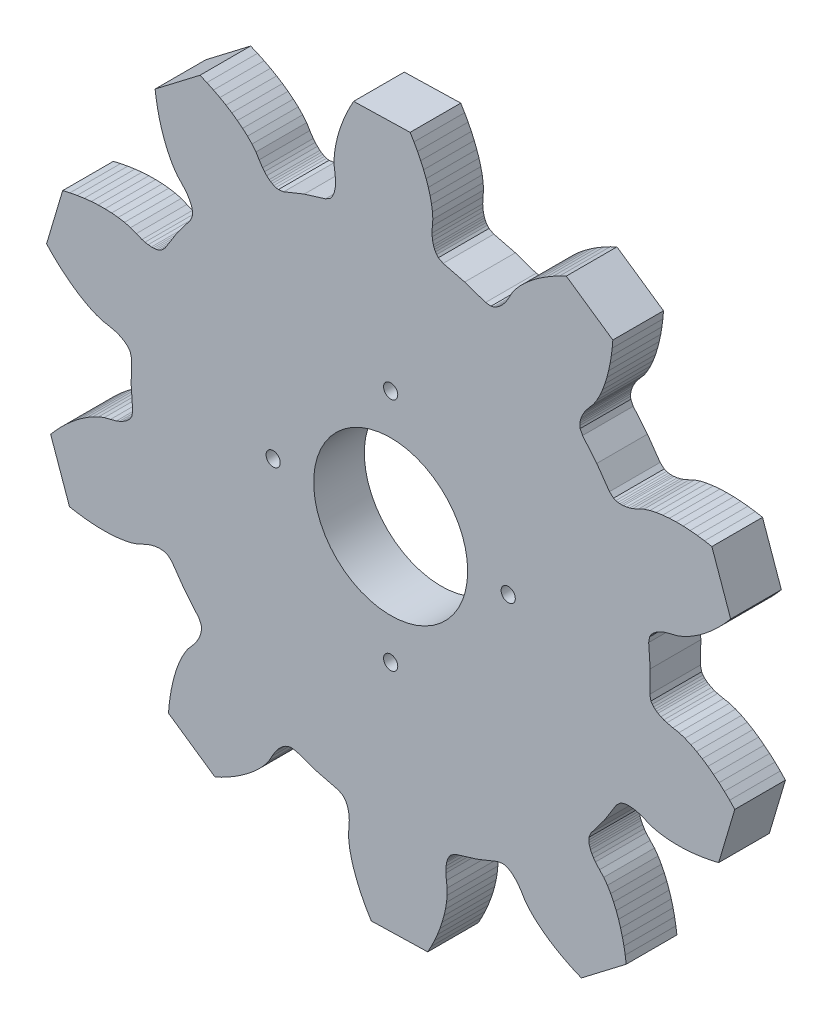
SolidWorks part; units mm, degrees
ref_plane "Front Plane" through (0, 0, 0) normal (0, 0, 1) x (1, 0, 0)
ref_plane "Top Plane" through (0, 0, 0) normal (0, 1, 0) x (1, 0, 0)
ref_plane "Right Plane" through (0, 0, 0) normal (1, 0, 0) x (0, 0, -1)
sketch "Sketch1" plane through (0, 0, 0) normal (0, 0, 1) x (1, 0, 0)
  line L2 (5.8044, 23.0223) -> (5.7313, 23.3545)
  line L3 (5.7313, 23.3545) -> (5.6459, 23.4886)
  line L4 (5.6459, 23.4886) -> (5.5583, 23.5882)
  line L5 (5.5583, 23.5882) -> (5.4694, 23.6692)
  line L6 (5.4694, 23.6692) -> (5.3795, 23.7376)
  line L7 (5.3795, 23.7376) -> (5.2888, 23.797)
  line L8 (5.2888, 23.797) -> (5.1059, 23.8948)
  line L9 (5.1059, 23.8948) -> (4.9207, 23.972)
  line L10 (4.9207, 23.972) -> (4.7338, 24.0332)
  line L11 (4.7338, 24.0332) -> (4.3561, 24.1183)
  line L12 (4.3561, 24.1183) -> (3.9766, 24.1866)
  line L13 (3.9766, 24.1866) -> (3.604, 24.3114)
  line L14 (3.604, 24.3114) -> (3.2362, 24.4721)
  line L15 (3.2362, 24.4721) -> (2.873, 24.6616)
  line L16 (2.873, 24.6616) -> (2.5143, 24.876)
  line L17 (2.5143, 24.876) -> (2.1605, 25.1137)
  line L18 (2.1605, 25.1137) -> (1.812, 25.3731)
  line L19 (1.812, 25.3731) -> (1.4691, 25.6527)
  line L20 (1.4691, 25.6527) -> (1.1323, 25.9524)
  line L21 (1.1323, 25.9524) -> (0.8016, 26.2707)
  line L22 (0.8016, 26.2707) -> (0.4778, 26.6078)
  line L23 (0.4778, 26.6078) -> (1.4874, 30.0037)
  line L24 (1.4874, 30.0037) -> (1.9428, 30.1089)
  line L25 (1.9428, 30.1089) -> (2.3937, 30.195)
  line L26 (2.3937, 30.195) -> (2.8397, 30.2616)
  line L27 (2.8397, 30.2616) -> (3.2796, 30.3085)
  line L28 (3.2796, 30.3085) -> (3.7132, 30.3355)
  line L29 (3.7132, 30.3355) -> (4.1394, 30.3411)
  line L30 (4.1394, 30.3411) -> (4.557, 30.3251)
  line L31 (4.557, 30.3251) -> (4.9647, 30.2852)
  line L32 (4.9647, 30.2852) -> (5.3604, 30.2189)
  line L33 (5.3604, 30.2189) -> (5.7409, 30.1196)
  line L34 (5.7409, 30.1196) -> (6.096, 29.9695)
  line L35 (6.096, 29.9695) -> (6.459, 29.8343)
  line L36 (6.459, 29.8343) -> (6.6487, 29.7835)
  line L37 (6.6487, 29.7835) -> (6.8461, 29.747)
  line L38 (6.8461, 29.747) -> (7.0528, 29.7289)
  line L39 (7.0528, 29.7289) -> (7.161, 29.7292)
  line L40 (7.161, 29.7292) -> (7.2738, 29.7373)
  line L41 (7.2738, 29.7373) -> (7.3924, 29.7566)
  line L42 (7.3924, 29.7566) -> (7.5204, 29.7922)
  line L43 (7.5204, 29.7922) -> (7.665, 29.858)
  line L44 (7.665, 29.858) -> (7.9078, 30.0962)
  line L45 (7.9078, 30.0962) -> (8.6457, 31.2717)
  line L46 (8.6457, 31.2717) -> (9.4811, 32.3804)
  line L47 (9.4811, 32.3804) -> (9.6172, 32.6921)
  line L48 (9.6172, 32.6921) -> (9.6271, 32.8506)
  line L49 (9.6271, 32.8506) -> (9.6149, 32.9827)
  line L50 (9.6149, 32.9827) -> (9.5905, 33.1005)
  line L51 (9.5905, 33.1005) -> (9.558, 33.2087)
  line L52 (9.558, 33.2087) -> (9.5194, 33.3101)
  line L53 (9.5194, 33.3101) -> (9.429, 33.4968)
  line L54 (9.429, 33.4968) -> (9.3246, 33.6682)
  line L55 (9.3246, 33.6682) -> (9.2093, 33.8275)
  line L56 (9.2093, 33.8275) -> (8.9538, 34.1183)
  line L57 (8.9538, 34.1183) -> (8.6868, 34.3967)
  line L58 (8.6868, 34.3967) -> (8.4587, 34.7165)
  line L59 (8.4587, 34.7165) -> (8.2555, 35.0629)
  line L60 (8.2555, 35.0629) -> (8.0731, 35.4294)
  line L61 (8.0731, 35.4294) -> (7.9091, 35.814)
  line L62 (7.9091, 35.814) -> (7.7627, 36.2141)
  line L63 (7.7627, 36.2141) -> (7.6332, 36.6286)
  line L64 (7.6332, 36.6286) -> (7.5202, 37.0566)
  line L65 (7.5202, 37.0566) -> (7.4237, 37.497)
  line L66 (7.4237, 37.497) -> (7.3434, 37.9489)
  line L67 (7.3434, 37.9489) -> (7.2794, 38.4119)
  line L68 (7.2794, 38.4119) -> (10.0924, 40.5658)
  line L69 (10.0924, 40.5658) -> (10.5225, 40.3832)
  line L70 (10.5225, 40.3832) -> (10.938, 40.1879)
  line L71 (10.938, 40.1879) -> (11.3378, 39.9796)
  line L72 (11.3378, 39.9796) -> (11.7216, 39.7589)
  line L73 (11.7216, 39.7589) -> (12.0881, 39.5257)
  line L74 (12.0881, 39.5257) -> (12.4361, 39.2801)
  line L75 (12.4361, 39.2801) -> (12.7645, 39.0215)
  line L76 (12.7645, 39.0215) -> (13.0708, 38.7497)
  line L77 (13.0708, 38.7497) -> (13.352, 38.4632)
  line L78 (13.352, 38.4632) -> (13.6014, 38.1597)
  line L79 (13.6014, 38.1597) -> (13.8006, 37.8292)
  line L80 (13.8006, 37.8292) -> (14.0147, 37.5067)
  line L81 (14.0147, 37.5067) -> (14.1384, 37.354)
  line L82 (14.1384, 37.354) -> (14.2766, 37.2085)
  line L83 (14.2766, 37.2085) -> (14.4333, 37.0723)
  line L84 (14.4333, 37.0723) -> (14.5209, 37.0088)
  line L85 (14.5209, 37.0088) -> (14.6169, 36.9491)
  line L86 (14.6169, 36.9491) -> (14.7244, 36.895)
  line L87 (14.7244, 36.895) -> (14.8486, 36.8485)
  line L88 (14.8486, 36.8485) -> (15.0043, 36.8168)
  line L89 (15.0043, 36.8168) -> (15.3408, 36.8668)
  line L90 (15.3408, 36.8668) -> (16.6289, 37.3842)
  line L91 (16.6289, 37.3842) -> (17.9563, 37.7899)
  line L92 (17.9563, 37.7899) -> (18.2496, 37.9621)
  line L93 (18.2496, 37.9621) -> (18.3507, 38.0848)
  line L94 (18.3507, 38.0848) -> (18.4186, 38.1988)
  line L95 (18.4186, 38.1988) -> (18.4681, 38.3083)
  line L96 (18.4681, 38.3083) -> (18.5054, 38.415)
  line L97 (18.5054, 38.415) -> (18.5336, 38.5196)
  line L98 (18.5336, 38.5196) -> (18.5702, 38.7238)
  line L99 (18.5702, 38.7238) -> (18.5864, 38.9237)
  line L100 (18.5864, 38.9237) -> (18.587, 39.1203)
  line L101 (18.587, 39.1203) -> (18.5511, 39.5059)
  line L102 (18.5511, 39.5059) -> (18.4988, 39.8879)
  line L103 (18.4988, 39.8879) -> (18.5024, 40.2811)
  line L104 (18.5024, 40.2811) -> (18.5415, 40.6804)
  line L105 (18.5415, 40.6804) -> (18.6093, 41.0845)
  line L106 (18.6093, 41.0845) -> (18.7028, 41.4917)
  line L107 (18.7028, 41.4917) -> (18.8194, 41.9016)
  line L108 (18.8194, 41.9016) -> (18.9583, 42.3131)
  line L109 (18.9583, 42.3131) -> (19.1183, 42.7258)
  line L110 (19.1183, 42.7258) -> (19.2992, 43.1389)
  line L111 (19.2992, 43.1389) -> (19.4998, 43.5516)
  line L112 (19.4998, 43.5516) -> (19.7203, 43.9638)
  line L113 (19.7203, 43.9638) -> (23.2621, 44.0527)
  line L114 (23.2621, 44.0527) -> (23.5029, 43.6522)
  line L115 (23.5029, 43.6522) -> (23.7241, 43.2501)
  line L116 (23.7241, 43.2501) -> (23.9253, 42.8465)
  line L117 (23.9253, 42.8465) -> (24.1059, 42.4426)
  line L118 (24.1059, 42.4426) -> (24.2651, 42.0385)
  line L119 (24.2651, 42.0385) -> (24.4025, 41.6352)
  line L120 (24.4025, 41.6352) -> (24.5161, 41.2328)
  line L121 (24.5161, 41.2328) -> (24.6042, 40.8328)
  line L122 (24.6042, 40.8328) -> (24.6634, 40.436)
  line L123 (24.6634, 40.436) -> (24.6868, 40.0436)
  line L124 (24.6868, 40.0436) -> (24.6535, 39.6593)
  line L125 (24.6535, 39.6593) -> (24.6372, 39.2725)
  line L126 (24.6372, 39.2725) -> (24.6477, 39.0761)
  line L127 (24.6477, 39.0761) -> (24.6738, 38.8772)
  line L128 (24.6738, 38.8772) -> (24.7205, 38.6751)
  line L129 (24.7205, 38.6751) -> (24.7541, 38.5722)
  line L130 (24.7541, 38.5722) -> (24.7967, 38.4675)
  line L131 (24.7967, 38.4675) -> (24.8516, 38.3606)
  line L132 (24.8516, 38.3606) -> (24.925, 38.2499)
  line L133 (24.925, 38.2499) -> (25.0322, 38.1325)
  line L134 (25.0322, 38.1325) -> (25.334, 37.9753)
  line L135 (25.334, 37.9753) -> (26.6802, 37.637)
  line L136 (26.6802, 37.637) -> (27.9926, 37.1848)
  line L137 (27.9926, 37.1848) -> (28.3309, 37.1518)
  line L138 (28.3309, 37.1518) -> (28.4848, 37.1914)
  line L139 (28.4848, 37.1914) -> (28.6067, 37.244)
  line L140 (28.6067, 37.244) -> (28.7111, 37.3035)
  line L141 (28.7111, 37.3035) -> (28.8041, 37.3677)
  line L142 (28.8041, 37.3677) -> (28.8884, 37.4358)
  line L143 (28.8884, 37.4358) -> (29.0383, 37.5796)
  line L144 (29.0383, 37.5796) -> (29.1689, 37.7317)
  line L145 (29.1689, 37.7317) -> (29.2847, 37.8905)
  line L146 (29.2847, 37.8905) -> (29.4823, 38.2234)
  line L147 (29.4823, 38.2234) -> (29.6647, 38.5633)
  line L148 (29.6647, 38.5633) -> (29.8983, 38.8793)
  line L149 (29.8983, 38.8793) -> (30.165, 39.1795)
  line L150 (30.165, 39.1795) -> (30.4574, 39.4663)
  line L151 (30.4574, 39.4663) -> (30.7724, 39.7411)
  line L152 (30.7724, 39.7411) -> (31.1076, 40.004)
  line L153 (31.1076, 40.004) -> (31.4617, 40.2552)
  line L154 (31.4617, 40.2552) -> (31.8338, 40.495)
  line L155 (31.8338, 40.495) -> (32.2229, 40.7228)
  line L156 (32.2229, 40.7228) -> (32.6278, 40.939)
  line L157 (32.6278, 40.939) -> (33.0484, 41.1427)
  line L158 (33.0484, 41.1427) -> (35.9661, 39.133)
  line L159 (35.9661, 39.133) -> (35.9255, 38.6674)
  line L160 (35.9255, 38.6674) -> (35.8681, 38.212)
  line L161 (35.8681, 38.212) -> (35.7937, 37.7673)
  line L162 (35.7937, 37.7673) -> (35.7022, 37.3342)
  line L163 (35.7022, 37.3342) -> (35.5938, 36.9136)
  line L164 (35.5938, 36.9136) -> (35.4675, 36.5067)
  line L165 (35.4675, 36.5067) -> (35.3233, 36.1145)
  line L166 (35.3233, 36.1145) -> (35.1594, 35.7391)
  line L167 (35.1594, 35.7391) -> (34.974, 35.3832)
  line L168 (34.974, 35.3832) -> (34.7622, 35.052)
  line L169 (34.7622, 35.052) -> (34.5095, 34.7607)
  line L170 (34.5095, 34.7607) -> (34.2689, 34.4574)
  line L171 (34.2689, 34.4574) -> (34.162, 34.2925)
  line L172 (34.162, 34.2925) -> (34.0662, 34.1163)
  line L173 (34.0662, 34.1163) -> (33.9852, 33.925)
  line L174 (33.9852, 33.925) -> (33.9517, 33.8219)
  line L175 (33.9517, 33.8219) -> (33.9247, 33.7121)
  line L176 (33.9247, 33.7121) -> (33.9065, 33.5935)
  line L177 (33.9065, 33.5935) -> (33.9006, 33.4609)
  line L178 (33.9006, 33.4609) -> (33.9187, 33.303)
  line L179 (33.9187, 33.303) -> (34.07, 32.9984)
  line L180 (34.07, 32.9984) -> (34.9603, 31.9334)
  line L181 (34.9603, 31.9334) -> (35.7563, 30.7962)
  line L182 (35.7563, 30.7962) -> (36.0106, 30.5704)
  line L183 (36.0106, 30.5704) -> (36.1584, 30.512)
  line L184 (36.1584, 30.512) -> (36.288, 30.4828)
  line L185 (36.288, 30.4828) -> (36.4076, 30.4696)
  line L186 (36.4076, 30.4696) -> (36.5204, 30.467)
  line L187 (36.5204, 30.467) -> (36.6286, 30.4724)
  line L188 (36.6286, 30.4724) -> (36.8343, 30.5008)
  line L189 (36.8343, 30.5008) -> (37.0294, 30.5473)
  line L190 (37.0294, 30.5473) -> (37.2166, 30.6075)
  line L191 (37.2166, 30.6075) -> (37.5722, 30.7607)
  line L192 (37.5722, 30.7607) -> (37.9194, 30.9286)
  line L193 (37.9194, 30.9286) -> (38.2941, 31.0467)
  line L194 (38.2941, 31.0467) -> (38.6862, 31.1328)
  line L195 (38.6862, 31.1328) -> (39.0914, 31.193)
  line L196 (39.0914, 31.193) -> (39.5077, 31.2303)
  line L197 (39.5077, 31.2303) -> (39.9334, 31.2458)
  line L198 (39.9334, 31.2458) -> (40.3677, 31.241)
  line L199 (40.3677, 31.241) -> (40.8097, 31.2161)
  line L200 (40.8097, 31.2161) -> (41.2582, 31.1719)
  line L201 (41.2582, 31.1719) -> (41.7131, 31.1086)
  line L202 (41.7131, 31.1086) -> (42.1731, 31.0264)
  line L203 (42.1731, 31.0264) -> (43.3522, 27.6855)
  line L204 (43.3522, 27.6855) -> (43.0456, 27.3327)
  line L205 (43.0456, 27.3327) -> (42.7314, 26.9982)
  line L206 (42.7314, 26.9982) -> (42.4099, 26.6819)
  line L207 (42.4099, 26.6819) -> (42.0814, 26.3853)
  line L208 (42.0814, 26.3853) -> (41.7464, 26.1089)
  line L209 (41.7464, 26.1089) -> (41.4053, 25.8536)
  line L210 (41.4053, 25.8536) -> (41.0578, 25.6215)
  line L211 (41.0578, 25.6215) -> (40.7045, 25.414)
  line L212 (40.7045, 25.414) -> (40.3454, 25.2349)
  line L213 (40.3454, 25.2349) -> (39.9793, 25.0916)
  line L214 (39.9793, 25.0916) -> (39.6037, 25.0043)
  line L215 (39.6037, 25.0043) -> (39.2308, 24.9004)
  line L216 (39.2308, 24.9004) -> (39.0474, 24.83)
  line L217 (39.0474, 24.83) -> (38.8663, 24.7434)
  line L218 (38.8663, 24.7434) -> (38.6883, 24.6365)
  line L219 (38.6883, 24.6365) -> (38.6009, 24.5727)
  line L220 (38.6009, 24.5727) -> (38.5145, 24.4998)
  line L221 (38.5145, 24.4998) -> (38.4297, 24.4145)
  line L222 (38.4297, 24.4145) -> (38.3471, 24.3106)
  line L223 (38.3471, 24.3106) -> (38.2689, 24.1724)
  line L224 (38.2689, 24.1724) -> (38.2125, 23.8369)
  line L225 (38.2125, 23.8369) -> (38.3065, 22.4521)
  line L226 (38.3065, 22.4521) -> (38.2821, 21.0642)
  line L227 (38.2821, 21.0642) -> (38.3553, 20.732)
  line L228 (38.3553, 20.732) -> (38.4406, 20.5979)
  line L229 (38.4406, 20.5979) -> (38.5282, 20.4983)
  line L230 (38.5282, 20.4983) -> (38.6171, 20.4173)
  line L231 (38.6171, 20.4173) -> (38.7071, 20.349)
  line L232 (38.7071, 20.349) -> (38.7977, 20.2895)
  line L233 (38.7977, 20.2895) -> (38.9806, 20.1917)
  line L234 (38.9806, 20.1917) -> (39.1658, 20.1145)
  line L235 (39.1658, 20.1145) -> (39.3527, 20.0533)
  line L236 (39.3527, 20.0533) -> (39.7304, 19.9682)
  line L237 (39.7304, 19.9682) -> (40.1099, 19.8999)
  line L238 (40.1099, 19.8999) -> (40.4825, 19.7752)
  line L239 (40.4825, 19.7752) -> (40.8503, 19.6144)
  line L240 (40.8503, 19.6144) -> (41.2135, 19.4249)
  line L241 (41.2135, 19.4249) -> (41.5722, 19.2105)
  line L242 (41.5722, 19.2105) -> (41.9257, 18.9728)
  line L243 (41.9257, 18.9728) -> (42.2745, 18.7134)
  line L244 (42.2745, 18.7134) -> (42.6174, 18.4338)
  line L245 (42.6174, 18.4338) -> (42.9542, 18.1341)
  line L246 (42.9542, 18.1341) -> (43.2849, 17.8158)
  line L247 (43.2849, 17.8158) -> (43.6088, 17.4788)
  line L248 (43.6088, 17.4788) -> (42.5988, 14.0828)
  line L249 (42.5988, 14.0828) -> (42.1437, 13.9776)
  line L250 (42.1437, 13.9776) -> (41.6928, 13.8915)
  line L251 (41.6928, 13.8915) -> (41.2468, 13.825)
  line L252 (41.2468, 13.825) -> (40.8069, 13.778)
  line L253 (40.8069, 13.778) -> (40.3733, 13.7511)
  line L254 (40.3733, 13.7511) -> (39.9471, 13.7455)
  line L255 (39.9471, 13.7455) -> (39.5295, 13.7615)
  line L256 (39.5295, 13.7615) -> (39.1218, 13.8013)
  line L257 (39.1218, 13.8013) -> (38.7261, 13.8676)
  line L258 (38.7261, 13.8676) -> (38.3456, 13.967)
  line L259 (38.3456, 13.967) -> (37.9905, 14.1171)
  line L260 (37.9905, 14.1171) -> (37.6276, 14.2522)
  line L261 (37.6276, 14.2522) -> (37.4378, 14.303)
  line L262 (37.4378, 14.303) -> (37.2405, 14.3396)
  line L263 (37.2405, 14.3396) -> (37.0337, 14.3576)
  line L264 (37.0337, 14.3576) -> (36.9255, 14.3574)
  line L265 (36.9255, 14.3574) -> (36.8127, 14.3492)
  line L266 (36.8127, 14.3492) -> (36.6941, 14.3299)
  line L267 (36.6941, 14.3299) -> (36.5661, 14.2944)
  line L268 (36.5661, 14.2944) -> (36.4216, 14.2286)
  line L269 (36.4216, 14.2286) -> (36.1787, 13.9903)
  line L270 (36.1787, 13.9903) -> (35.4409, 12.8148)
  line L271 (35.4409, 12.8148) -> (34.6055, 11.7061)
  line L272 (34.6055, 11.7061) -> (34.4693, 11.3944)
  line L273 (34.4693, 11.3944) -> (34.4594, 11.2359)
  line L274 (34.4594, 11.2359) -> (34.4716, 11.1039)
  line L275 (34.4716, 11.1039) -> (34.496, 10.986)
  line L276 (34.496, 10.986) -> (34.5285, 10.8778)
  line L277 (34.5285, 10.8778) -> (34.5671, 10.7765)
  line L278 (34.5671, 10.7765) -> (34.6575, 10.5898)
  line L279 (34.6575, 10.5898) -> (34.7619, 10.4183)
  line L280 (34.7619, 10.4183) -> (34.8772, 10.2591)
  line L281 (34.8772, 10.2591) -> (35.1328, 9.9682)
  line L282 (35.1328, 9.9682) -> (35.3997, 9.6898)
  line L283 (35.3997, 9.6898) -> (35.6278, 9.3701)
  line L284 (35.6278, 9.3701) -> (35.831, 9.0236)
  line L285 (35.831, 9.0236) -> (36.0134, 8.6571)
  line L286 (36.0134, 8.6571) -> (36.1775, 8.2725)
  line L287 (36.1775, 8.2725) -> (36.3238, 7.8725)
  line L288 (36.3238, 7.8725) -> (36.4533, 7.4579)
  line L289 (36.4533, 7.4579) -> (36.5663, 7.03)
  line L290 (36.5663, 7.03) -> (36.6629, 6.5895)
  line L291 (36.6629, 6.5895) -> (36.7431, 6.1377)
  line L292 (36.7431, 6.1377) -> (36.8071, 5.6746)
  line L293 (36.8071, 5.6746) -> (33.9941, 3.5207)
  line L294 (33.9941, 3.5207) -> (33.5641, 3.7033)
  line L295 (33.5641, 3.7033) -> (33.1485, 3.8986)
  line L296 (33.1485, 3.8986) -> (32.7487, 4.1069)
  line L297 (32.7487, 4.1069) -> (32.3649, 4.3274)
  line L298 (32.3649, 4.3274) -> (31.9984, 4.5608)
  line L299 (31.9984, 4.5608) -> (31.6504, 4.8064)
  line L300 (31.6504, 4.8064) -> (31.322, 5.065)
  line L301 (31.322, 5.065) -> (31.0157, 5.3368)
  line L302 (31.0157, 5.3368) -> (30.7345, 5.6233)
  line L303 (30.7345, 5.6233) -> (30.4851, 5.9268)
  line L304 (30.4851, 5.9268) -> (30.2859, 6.2573)
  line L305 (30.2859, 6.2573) -> (30.0718, 6.5799)
  line L306 (30.0718, 6.5799) -> (29.9481, 6.7325)
  line L307 (29.9481, 6.7325) -> (29.8099, 6.8781)
  line L308 (29.8099, 6.8781) -> (29.6532, 7.0142)
  line L309 (29.6532, 7.0142) -> (29.5656, 7.0777)
  line L310 (29.5656, 7.0777) -> (29.4696, 7.1374)
  line L311 (29.4696, 7.1374) -> (29.3621, 7.1915)
  line L312 (29.3621, 7.1915) -> (29.2379, 7.238)
  line L313 (29.2379, 7.238) -> (29.0822, 7.2697)
  line L314 (29.0822, 7.2697) -> (28.7457, 7.2197)
  line L315 (28.7457, 7.2197) -> (27.4577, 6.7023)
  line L316 (27.4577, 6.7023) -> (26.1303, 6.2967)
  line L317 (26.1303, 6.2967) -> (25.8369, 6.1244)
  line L318 (25.8369, 6.1244) -> (25.7358, 6.0018)
  line L319 (25.7358, 6.0018) -> (25.668, 5.8877)
  line L320 (25.668, 5.8877) -> (25.6184, 5.7782)
  line L321 (25.6184, 5.7782) -> (25.5811, 5.6716)
  line L322 (25.5811, 5.6716) -> (25.5529, 5.5669)
  line L323 (25.5529, 5.5669) -> (25.5163, 5.3627)
  line L324 (25.5163, 5.3627) -> (25.5001, 5.1628)
  line L325 (25.5001, 5.1628) -> (25.4996, 4.9662)
  line L326 (25.4996, 4.9662) -> (25.5354, 4.5806)
  line L327 (25.5354, 4.5806) -> (25.5877, 4.1986)
  line L328 (25.5877, 4.1986) -> (25.5842, 3.8054)
  line L329 (25.5842, 3.8054) -> (25.545, 3.4061)
  line L330 (25.545, 3.4061) -> (25.4772, 3.002)
  line L331 (25.4772, 3.002) -> (25.3837, 2.5949)
  line L332 (25.3837, 2.5949) -> (25.2672, 2.1849)
  line L333 (25.2672, 2.1849) -> (25.1282, 1.7734)
  line L334 (25.1282, 1.7734) -> (24.9682, 1.3607)
  line L335 (24.9682, 1.3607) -> (24.7874, 0.9477)
  line L336 (24.7874, 0.9477) -> (24.5867, 0.5349)
  line L337 (24.5867, 0.5349) -> (24.3662, 0.1227)
  line L338 (24.3662, 0.1227) -> (20.8244, 0.0338)
  line L339 (20.8244, 0.0338) -> (20.5837, 0.4343)
  line L340 (20.5837, 0.4343) -> (20.3624, 0.8364)
  line L341 (20.3624, 0.8364) -> (20.1612, 1.24)
  line L342 (20.1612, 1.24) -> (19.9807, 1.6439)
  line L343 (19.9807, 1.6439) -> (19.8214, 2.048)
  line L344 (19.8214, 2.048) -> (19.684, 2.4514)
  line L345 (19.684, 2.4514) -> (19.5704, 2.8537)
  line L346 (19.5704, 2.8537) -> (19.4823, 3.2537)
  line L347 (19.4823, 3.2537) -> (19.4231, 3.6505)
  line L348 (19.4231, 3.6505) -> (19.3998, 4.0429)
  line L349 (19.3998, 4.0429) -> (19.433, 4.4272)
  line L350 (19.433, 4.4272) -> (19.4493, 4.8141)
  line L351 (19.4493, 4.8141) -> (19.4389, 5.0104)
  line L352 (19.4389, 5.0104) -> (19.4127, 5.209)
  line L353 (19.4127, 5.209) -> (19.366, 5.4115)
  line L354 (19.366, 5.4115) -> (19.3324, 5.5143)
  line L355 (19.3324, 5.5143) -> (19.2898, 5.619)
  line L356 (19.2898, 5.619) -> (19.2349, 5.7259)
  line L357 (19.2349, 5.7259) -> (19.1615, 5.8367)
  line L358 (19.1615, 5.8367) -> (19.0543, 5.954)
  line L359 (19.0543, 5.954) -> (18.7526, 6.1112)
  line L360 (18.7526, 6.1112) -> (17.4064, 6.4496)
  line L361 (17.4064, 6.4496) -> (16.0939, 6.9017)
  line L362 (16.0939, 6.9017) -> (15.7556, 6.9347)
  line L363 (15.7556, 6.9347) -> (15.6017, 6.8951)
  line L364 (15.6017, 6.8951) -> (15.4798, 6.8425)
  line L365 (15.4798, 6.8425) -> (15.3754, 6.7831)
  line L366 (15.3754, 6.7831) -> (15.2824, 6.7188)
  line L367 (15.2824, 6.7188) -> (15.1981, 6.6507)
  line L368 (15.1981, 6.6507) -> (15.0482, 6.507)
  line L369 (15.0482, 6.507) -> (14.9177, 6.3548)
  line L370 (14.9177, 6.3548) -> (14.8018, 6.1961)
  line L371 (14.8018, 6.1961) -> (14.6042, 5.8631)
  line L372 (14.6042, 5.8631) -> (14.4219, 5.5232)
  line L373 (14.4219, 5.5232) -> (14.1882, 5.2073)
  line L374 (14.1882, 5.2073) -> (13.9215, 4.907)
  line L375 (13.9215, 4.907) -> (13.6291, 4.6203)
  line L376 (13.6291, 4.6203) -> (13.3142, 4.3454)
  line L377 (13.3142, 4.3454) -> (12.9789, 4.0825)
  line L378 (12.9789, 4.0825) -> (12.6248, 3.8313)
  line L379 (12.6248, 3.8313) -> (12.2527, 3.5916)
  line L380 (12.2527, 3.5916) -> (11.8636, 3.3637)
  line L381 (11.8636, 3.3637) -> (11.4587, 3.1476)
  line L382 (11.4587, 3.1476) -> (11.0381, 2.9439)
  line L383 (11.0381, 2.9439) -> (8.1204, 4.9535)
  line L384 (8.1204, 4.9535) -> (8.161, 5.4191)
  line L385 (8.161, 5.4191) -> (8.2184, 5.8745)
  line L386 (8.2184, 5.8745) -> (8.2928, 6.3193)
  line L387 (8.2928, 6.3193) -> (8.3843, 6.7523)
  line L388 (8.3843, 6.7523) -> (8.4927, 7.173)
  line L389 (8.4927, 7.173) -> (8.619, 7.5799)
  line L390 (8.619, 7.5799) -> (8.7633, 7.972)
  line L391 (8.7633, 7.972) -> (8.9271, 8.3475)
  line L392 (8.9271, 8.3475) -> (9.1125, 8.7033)
  line L393 (9.1125, 8.7033) -> (9.3243, 9.0345)
  line L394 (9.3243, 9.0345) -> (9.5771, 9.3259)
  line L395 (9.5771, 9.3259) -> (9.8176, 9.6291)
  line L396 (9.8176, 9.6291) -> (9.9245, 9.794)
  line L397 (9.9245, 9.794) -> (10.0203, 9.9703)
  line L398 (10.0203, 9.9703) -> (10.1013, 10.1615)
  line L399 (10.1013, 10.1615) -> (10.1349, 10.2646)
  line L400 (10.1349, 10.2646) -> (10.1618, 10.3744)
  line L401 (10.1618, 10.3744) -> (10.1801, 10.493)
  line L402 (10.1801, 10.493) -> (10.1859, 10.6256)
  line L403 (10.1859, 10.6256) -> (10.1679, 10.7836)
  line L404 (10.1679, 10.7836) -> (10.0165, 11.0881)
  line L405 (10.0165, 11.0881) -> (9.1262, 12.1531)
  line L406 (9.1262, 12.1531) -> (8.3302, 13.2903)
  line L407 (8.3302, 13.2903) -> (8.0759, 13.5161)
  line L408 (8.0759, 13.5161) -> (7.9281, 13.5745)
  line L409 (7.9281, 13.5745) -> (7.7986, 13.6035)
  line L410 (7.7986, 13.6035) -> (7.6789, 13.6169)
  line L411 (7.6789, 13.6169) -> (7.5662, 13.6195)
  line L412 (7.5662, 13.6195) -> (7.4579, 13.6141)
  line L413 (7.4579, 13.6141) -> (7.2522, 13.5857)
  line L414 (7.2522, 13.5857) -> (7.0571, 13.5392)
  line L415 (7.0571, 13.5392) -> (6.8699, 13.479)
  line L416 (6.8699, 13.479) -> (6.5143, 13.3259)
  line L417 (6.5143, 13.3259) -> (6.1671, 13.158)
  line L418 (6.1671, 13.158) -> (5.7925, 13.0399)
  line L419 (5.7925, 13.0399) -> (5.4003, 12.9537)
  line L420 (5.4003, 12.9537) -> (4.9952, 12.8935)
  line L421 (4.9952, 12.8935) -> (4.5789, 12.8562)
  line L422 (4.5789, 12.8562) -> (4.1532, 12.8407)
  line L423 (4.1532, 12.8407) -> (3.7188, 12.8455)
  line L424 (3.7188, 12.8455) -> (3.2769, 12.8704)
  line L425 (3.2769, 12.8704) -> (2.8283, 12.9146)
  line L426 (2.8283, 12.9146) -> (2.3734, 12.9779)
  line L427 (2.3734, 12.9779) -> (1.9134, 13.0602)
  line L428 (1.9134, 13.0602) -> (0.7343, 16.401)
  line L429 (0.7343, 16.401) -> (1.0409, 16.7538)
  line L430 (1.0409, 16.7538) -> (1.3551, 17.0884)
  line L431 (1.3551, 17.0884) -> (1.6767, 17.4046)
  line L432 (1.6767, 17.4046) -> (2.0051, 17.7013)
  line L433 (2.0051, 17.7013) -> (2.3401, 17.9776)
  line L434 (2.3401, 17.9776) -> (2.6812, 18.2329)
  line L435 (2.6812, 18.2329) -> (3.0287, 18.465)
  line L436 (3.0287, 18.465) -> (3.382, 18.6726)
  line L437 (3.382, 18.6726) -> (3.7412, 18.8516)
  line L438 (3.7412, 18.8516) -> (4.1072, 18.9949)
  line L439 (4.1072, 18.9949) -> (4.4828, 19.0823)
  line L440 (4.4828, 19.0823) -> (4.8557, 19.1861)
  line L441 (4.8557, 19.1861) -> (5.0391, 19.2565)
  line L442 (5.0391, 19.2565) -> (5.2202, 19.3429)
  line L443 (5.2202, 19.3429) -> (5.3983, 19.4501)
  line L444 (5.3983, 19.4501) -> (5.4856, 19.5138)
  line L445 (5.4856, 19.5138) -> (5.572, 19.5867)
  line L446 (5.572, 19.5867) -> (5.6568, 19.672)
  line L447 (5.6568, 19.672) -> (5.7394, 19.7759)
  line L448 (5.7394, 19.7759) -> (5.8176, 19.9141)
  line L449 (5.8176, 19.9141) -> (5.874, 20.2496)
  line L450 (5.874, 20.2496) -> (5.78, 21.6345)
  line L451 (5.78, 21.6345) -> (5.8044, 23.0223)
  circle A0 centre (22.0431, 22.0431) radius 4.826
extrude "Boss-Extrude1" add sketch "Sketch1" along normal blind 3.175
sketch "Sketch2" plane through (0, 0, 3.175) normal (0, 0, 1) x (1, 0, 0)
  line L0 (22.0431, 22.0431) -> (14.6771, 22.0431) construction
  circle A0 centre (14.6771, 22.0431) radius 0.4445
  dimension "D2" = 0.889
  dimension "D1" = 7.366
extrude "Cut-Extrude1" cut sketch "Sketch2" against normal through all
pattern_circular "CirPattern1" count 4 over 360 about axis through (22.0431, 22.0431, 0) along (0, 0, 1) of "Cut-Extrude1"
